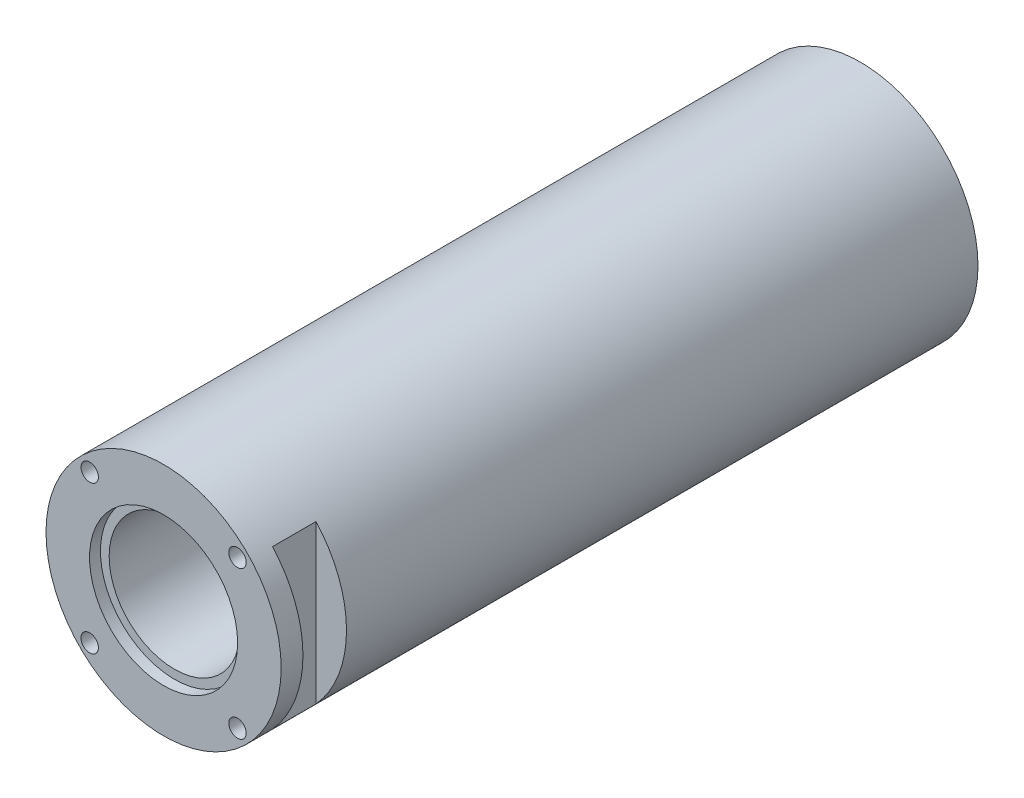
SolidWorks part; units mm, degrees
ref_plane "Plan de face" through (0, 0, 0) normal (0, 0, 1) x (1, 0, 0)
ref_plane "Plan de dessus" through (0, 0, 0) normal (0, 1, 0) x (1, 0, 0)
ref_plane "Plan de droite" through (0, 0, 0) normal (1, 0, 0) x (0, 0, -1)
sketch "Esquisse1" plane through (0, 0, 0) normal (0, 0, 1) x (1, 0, 0)
  circle A0 centre (0, 0) radius 15
  circle A1 centre (0, 0) radius 27
extrude "Extrusion1" add sketch "Esquisse1" along normal blind 160
sketch "Esquisse2" plane through (0, 0, 160) normal (0, 0, 1) x (1, 0, 0)
  line L1 (-0.0005, 0.0005) -> (16.97, 16.9711) construction
  circle A4 centre (16.97, 16.9711) radius 2
  circle A5 centre (16.97, -16.97) radius 2
  circle A6 centre (-16.9711, -16.97) radius 2
  circle A7 centre (-16.9711, 16.9711) radius 2
extrude "Extrusion2" cut sketch "Esquisse2" against normal blind 15
sketch "Esquisse3" plane through (0, 0, 0) normal (0, 0, -1) x (-1, 0, 0)
  line L0 (0, 0) -> (0, 24) construction
  circle A4 centre (16.97, 16.9711) radius 2
  circle A5 centre (-16.9711, 16.9711) radius 2
  circle A6 centre (-16.9711, -16.97) radius 2
  circle A7 centre (16.97, -16.97) radius 2
extrude "Extrusion3" cut sketch "Esquisse3" against normal blind 15
sketch "Esquisse4" plane through (0, 0, 160) normal (0, 0, 1) x (1, 0, 0)
  circle A0 centre (0, 0) radius 17
  circle A1 centre (0, 0) radius 15
extrude "Extrusion4" cut sketch "Esquisse4" against normal blind 2.5
sketch "Esquisse5" plane through (0, 0, 0) normal (0, 0, -1) x (-1, 0, 0)
  circle A0 centre (0, 0) radius 17
  circle A1 centre (0, 0) radius 15
extrude "Extrusion5" cut sketch "Esquisse5" against normal blind 2.5
sketch "Esquisse6" plane through (0, 0, 0) normal (1, 0, 0) x (0, 0, -1)
  line L1 (-160, -27) -> (0, -27) construction
  line L2 (-140, -21) -> (-20, -21)
  line L3 (-20, -21) -> (-20, -27)
  line L4 (-140, -21) -> (-140, -27)
  line L5 (-20, -27) -> (-140, -27)
  line L6 (-160, 0) -> (-112.7212, 0) construction
  line L7 (-160, 27) -> (-160, -27) construction
extrude "Extrusion6" cut sketch "Esquisse6" against normal through all and the other way through all
sketch "Esquisse7" plane through (0, 0, 0) normal (0, 1, 0) x (1, 0, 0)
  line L0 (27, -155) -> (20, -155)
  line L1 (27, -145) -> (20, -145)
  line L4 (27, -160) -> (27, 0) construction
  line L5 (27, -155) -> (27, -145)
  line L7 (20, -145) -> (20, -155)
  line L8 (-20, -145) -> (-20, -155)
  line L9 (-27, -155) -> (-27, -145)
  line L10 (-27, -145) -> (-20, -145)
  line L11 (-27, -155) -> (-20, -155)
extrude "Extrusion7" cut sketch "Esquisse7" against normal through all and the other way through all
